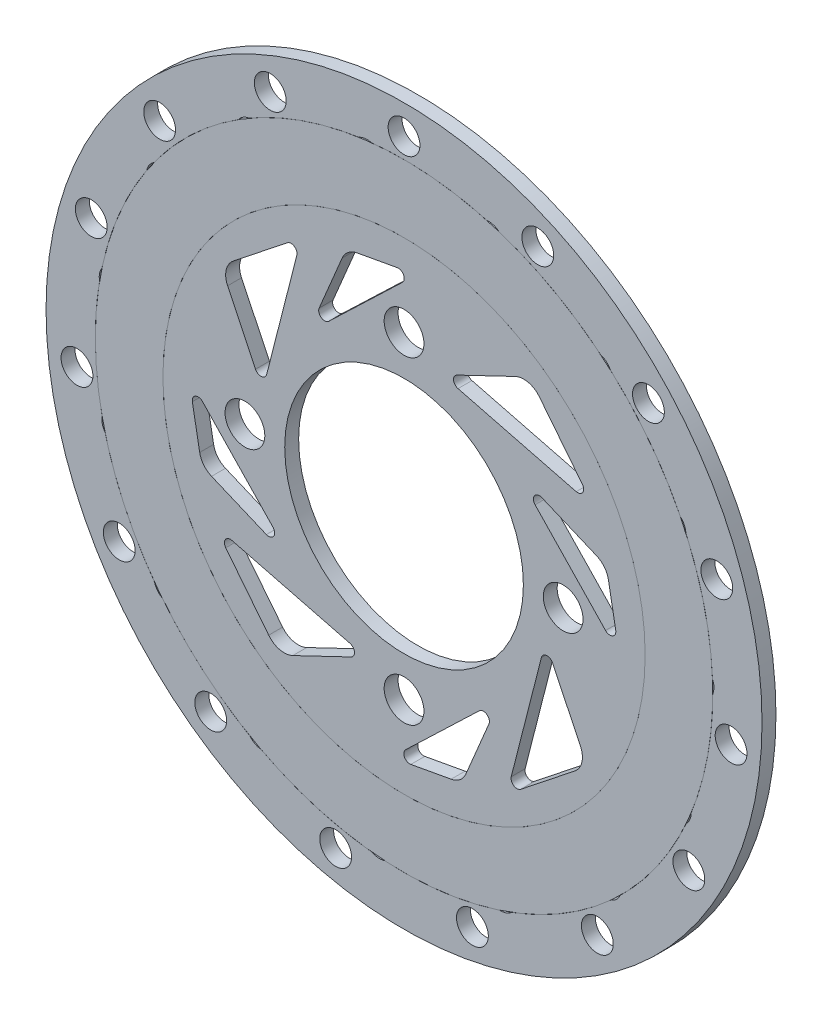
SolidWorks part; units mm, degrees
material "Malleable Cast Iron"
ref_plane "Front Plane" through (0, 0, 0) normal (0, 0, 1) x (1, 0, 0)
ref_plane "Top Plane" through (0, 0, 0) normal (0, 1, 0) x (1, 0, 0)
ref_plane "Right Plane" through (0, 0, 0) normal (1, 0, 0) x (0, 0, -1)
sketch "Sketch1" plane through (0, 0, 0) normal (0, 0, 1) x (1, 0, 0)
  line L0 (-75.9233, 33.5266) -> (-82.9451, 48.1802)
  line L1 (-73.1171, 33.804) -> (-65.537, 63.5161)
  line L2 (-81.5432, 54.2582) -> (-67.9226, 65.0621)
  line L3 (-25.0192, 54.76) -> (4.6929, 47.1799)
  line L4 (-4.565, 63.1861) -> (6.2389, 49.5655)
  line L5 (-25.2966, 57.5661) -> (-10.6429, 64.5879)
  line L6 (-4.0632, 6.6621) -> (-11.6433, -23.05)
  line L7 (4.3629, -13.7922) -> (-9.2577, -24.596)
  line L8 (-1.2571, 6.9395) -> (5.7647, -7.7142)
  line L9 (-52.1611, -14.2939) -> (-81.8732, -6.7138)
  line L10 (-72.6153, -22.72) -> (-83.4192, -9.0994)
  line L11 (-51.8837, -17.1001) -> (-66.5374, -24.1219)
  line L12 (-50.4308, 71.6048) -> (-40.3064, 73.454)
  line L13 (12.7816, 32.0737) -> (14.6308, 21.9492)
  line L14 (-5.6494, 39.1532) -> (12.0717, 20.6424)
  line L15 (-59.9306, 54.8381) -> (-54.1425, 68.6221)
  line L16 (-57.5103, 53.1738) -> (-38.9995, 70.8949)
  line L17 (-3.9851, 41.5735) -> (9.7989, 35.7853)
  line L18 (-26.7495, -31.1388) -> (-36.874, -32.988)
  line L19 (-19.67, -12.7077) -> (-38.1808, -30.4289)
  line L20 (-17.2497, -14.372) -> (-23.0378, -28.156)
  line L21 (-89.962, 8.3924) -> (-91.8112, 18.5168)
  line L22 (-71.5309, 1.3129) -> (-89.2521, 19.8237)
  line L23 (-73.1952, -1.1074) -> (-86.9792, 4.6807)
  circle A0 centre (-38.5902, 20.233) radius 90
  circle A1 centre (-38.5902, 20.233) radius 30
  circle A2 centre (-38.5902, 60.233) radius 5
  circle A3 centre (-78.5902, 20.233) radius 5
  circle A4 centre (-38.5902, -19.767) radius 5
  circle A5 centre (1.4098, 20.233) radius 5
  circle A7 centre (-38.5902, 102.9089) radius 4
  circle A8 centre (-57.2722, 84.2268) radius 4.1639
  circle A9 centre (-47.9312, 93.5678) radius 4
  circle A10 centre (-29.6285, 86.2929) radius 4.1639
  circle A11 centre (-17.2957, 91.027) radius 4
  circle A12 centre (-4.9629, 95.7612) radius 4
  circle A13 centre (-3.5343, 76.9367) radius 4.1639
  circle A14 centre (9.6578, 76.2453) radius 4
  circle A15 centre (22.85, 75.554) radius 4
  circle A16 centre (16.4984, 57.7759) radius 4.1639
  circle A17 centre (28.2688, 51.7786) radius 4
  circle A18 centre (40.0392, 45.7813) radius 4
  circle A19 centre (27.0058, 32.1236) radius 4.1639
  circle A20 centre (35.3193, 21.8573) radius 4
  circle A21 centre (43.6328, 11.5911) radius 4
  circle A22 centre (26.1711, 4.4153) radius 4.1639
  circle A23 centre (29.5901, -8.3448) radius 4
  circle A24 centre (33.0092, -21.1049) radius 4
  circle A25 centre (14.1385, -20.5579) radius 4.1639
  circle A26 centre (12.072, -33.6055) radius 4
  circle A27 centre (10.0055, -46.6531) radius 4
  circle A28 centre (-7.0113, -38.4781) radius 4.1639
  circle A29 centre (-14.2061, -49.5571) radius 4
  circle A30 centre (-21.4009, -60.6361) radius 4
  circle A31 centre (-33.6214, -46.2465) radius 4.1639
  circle A32 centre (-44.7004, -53.4413) radius 4
  circle A33 centre (-55.7794, -60.6361) radius 4
  circle A34 centre (-61.0906, -42.52) radius 4.1639
  circle A35 centre (-74.1382, -44.5866) radius 4
  circle A36 centre (-87.1858, -46.6531) radius 4
  circle A37 centre (-84.6693, -27.943) radius 4.1639
  circle A38 centre (-97.4294, -24.5239) radius 4
  circle A39 centre (-110.1895, -21.1049) radius 4
  circle A40 centre (-100.2805, -5.0359) radius 4.1639
  circle A41 centre (-110.5468, 3.2776) radius 4
  circle A42 centre (-120.8131, 11.5911) radius 4
  circle A43 centre (-105.2249, 22.2405) radius 4.1639
  circle A44 centre (-111.2222, 34.0109) radius 4
  circle A45 centre (-117.2195, 45.7813) radius 4
  circle A46 centre (-98.6475, 49.1697) radius 4.1639
  circle A47 centre (-99.3389, 62.3618) radius 4
  circle A48 centre (-100.0303, 75.554) radius 4
  circle A49 centre (-81.6857, 71.0956) radius 4.1639
  circle A50 centre (-76.9516, 83.4284) radius 4
  circle A51 centre (-72.2174, 95.7612) radius 4
  arc A52 (-75.9233, 33.5266) -> (-73.1171, 33.804) centre (-74.5705, 34.1748) ccw
  arc A53 (-65.537, 63.5161) -> (-67.9226, 65.0621) centre (-66.9905, 63.8869) ccw
  arc A54 (-82.9451, 48.1802) -> (-81.5432, 54.2582) centre (-78.436, 50.3409) cw
  arc A55 (-25.2966, 57.5661) -> (-25.0192, 54.76) centre (-24.6484, 56.2134) ccw
  arc A56 (4.6929, 47.1799) -> (6.2389, 49.5655) centre (5.0637, 48.6333) ccw
  arc A57 (-10.6429, 64.5879) -> (-4.565, 63.1861) centre (-8.4823, 60.0789) cw
  arc A58 (-1.2571, 6.9395) -> (-4.0632, 6.6621) centre (-2.6098, 6.2913) ccw
  arc A59 (-11.6433, -23.05) -> (-9.2577, -24.596) centre (-10.1899, -23.4208) ccw
  arc A60 (5.7647, -7.7142) -> (4.3629, -13.7922) centre (1.2557, -9.8748) cw
  arc A61 (-51.8837, -17.1001) -> (-52.1611, -14.2939) centre (-52.5319, -15.7473) ccw
  arc A62 (-81.8732, -6.7138) -> (-83.4192, -9.0994) centre (-82.244, -8.1673) ccw
  arc A63 (-66.5374, -24.1219) -> (-72.6153, -22.72) centre (-68.698, -19.6128) cw
  arc A64 (-59.9306, 54.8381) -> (-57.5103, 53.1738) centre (-58.5476, 54.2573) ccw
  arc A65 (-38.9995, 70.8949) -> (-40.3064, 73.454) centre (-40.0368, 71.9785) ccw
  arc A66 (-50.4308, 71.6048) -> (-54.1425, 68.6221) centre (-49.5324, 66.6862) ccw
  arc A67 (12.0717, 20.6424) -> (14.6308, 21.9492) centre (13.1553, 21.6797) ccw
  arc A68 (12.7816, 32.0737) -> (9.7989, 35.7853) centre (7.863, 31.1753) ccw
  arc A69 (-3.9851, 41.5735) -> (-5.6494, 39.1532) centre (-4.5659, 40.1905) ccw
  arc A70 (-38.1808, -30.4289) -> (-36.874, -32.988) centre (-37.1435, -31.5124) ccw
  arc A71 (-26.7495, -31.1388) -> (-23.0378, -28.156) centre (-27.6479, -26.2201) ccw
  arc A72 (-17.2497, -14.372) -> (-19.67, -12.7077) centre (-18.6327, -13.7913) ccw
  arc A73 (-89.2521, 19.8237) -> (-91.8112, 18.5168) centre (-90.3356, 18.7864) ccw
  arc A74 (-89.962, 8.3924) -> (-86.9792, 4.6807) centre (-85.0433, 9.2908) ccw
  arc A75 (-73.1952, -1.1074) -> (-71.5309, 1.3129) centre (-72.6144, 0.2756) ccw
  point P104 (-38.5902, 20.233)
  point P113 (-38.5899, 20.2248)
  point P143 (-38.5902, 20.233)
  point P180 (-38.5902, 20.233)
  dimension "D1" = 10
  dimension "D2" = 10
  dimension "D3" = 15
  dimension "D4" = 180
  dimension "D5" = 1.5
  dimension "D6" = 5
  dimension "D8" = 1.5
  dimension "D9" = 5
  dimension "D11" = 80
  dimension "D7" = 4
  dimension "D10" = 4
extrude "Boss-Extrude1" add sketch "Sketch1" along normal blind 3.5
sketch "Sketch3" plane through (0, 0, 0) normal (0, 0, -1) x (-1, 0, 0)
  circle A0 centre (38.5902, 20.233) radius 60.6166
  circle A1 centre (38.5902, 20.233) radius 77.6116
extrude "Boss-Extrude2" add sketch "Sketch3" against normal blind 3.501 and the other way blind 0.001
